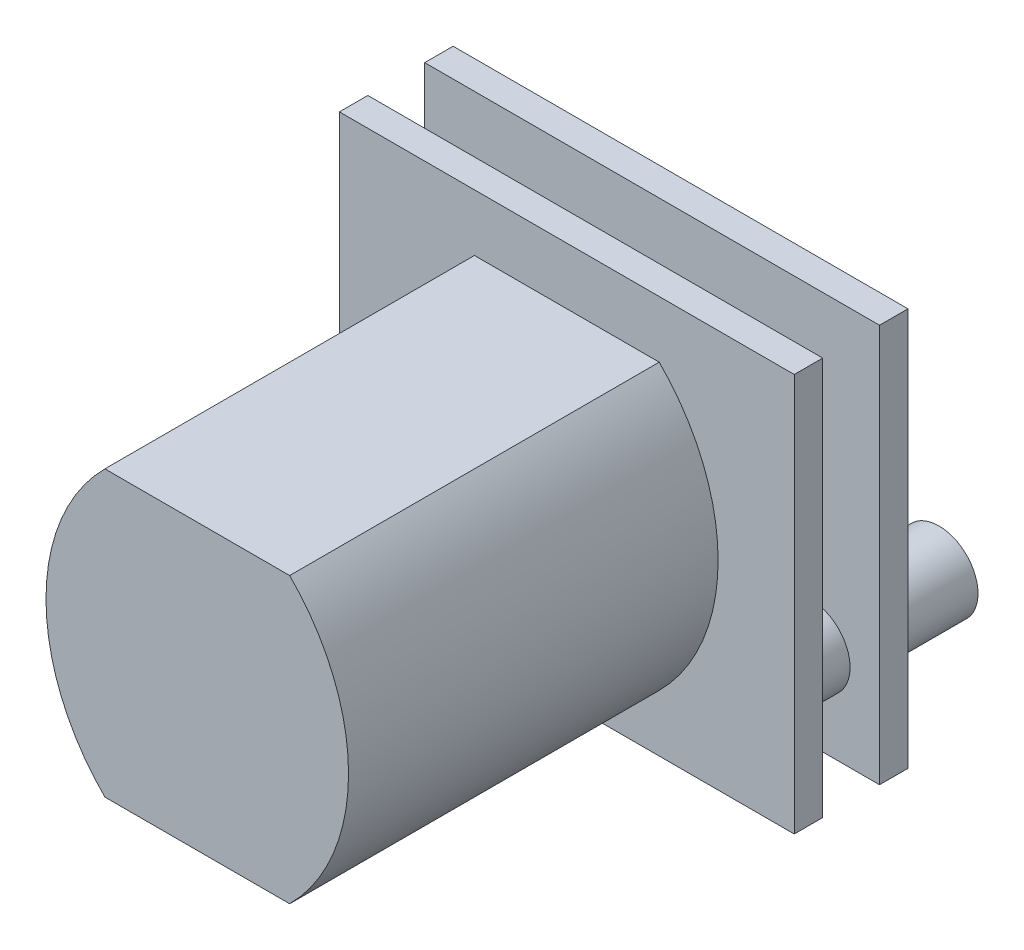
SolidWorks part; units mm, degrees
ref_plane "Front Plane" through (0, 0, 0) normal (0, 0, 1) x (1, 0, 0)
ref_plane "Top Plane" through (0, 0, 0) normal (0, 1, 0) x (1, 0, 0)
ref_plane "Right Plane" through (0, 0, 0) normal (1, 0, 0) x (0, 0, -1)
sketch "Sketch1" plane through (0, 0, 0) normal (0, 0, 1) x (1, 0, 0)
  line L0 (0, 0) -> (0, -50000) construction
  line L1 (-3.25, 5) -> (3.25, 5)
  line L3 (-3.25, -5) -> (3.25, -5)
  line L5 (-3.25, 5) -> (3.25, -5) construction
  line L6 (-3.25, -5) -> (3.25, 5) construction
  arc A0 (3.25, -5) -> (3.25, 5) centre (-1.75, 0) ccw
  arc A1 (-3.25, -5) -> (-3.25, 5) centre (1.75, 0) cw
  point P0 (0, 0)
  dimension "D1" = 6.5
  dimension "D2" = 10
extrude "Extrude1" add sketch "Sketch1" along normal blind 13
sketch "Sketch2" plane through (0, 0, 0) normal (0, 0, -1) x (-1, 0, 0)
  line L1 (8, -7) -> (-8, -7)
  line L2 (8, -7) -> (8, 7)
  line L3 (8, 7) -> (-8, 7)
  line L4 (-8, -7) -> (-8, 7)
  line L5 (8, -7) -> (-8, 7) construction
  line L6 (8, 7) -> (-8, -7) construction
  point P0 (0, 0)
  dimension "D1" = 8
  dimension "D2" = 7
extrude "Extrude2" add sketch "Sketch2" along normal blind 1
sketch "Sketch3" plane through (0, 0, -1) normal (0, 0, -1) x (-1, 0, 0)
  circle A0 centre (0, 0) radius 2.2487
extrude "Extrude3" add sketch "Sketch3" along normal blind 1.2
sketch "Sketch4" plane through (0, 0, -2.2) normal (0, 0, -1) x (-1, 0, 0)
  line L0 (-0.4598, -1.9553) -> (-0.6222, -2.4282)
  line L1 (0.2, -1.9987) -> (-0.2, -1.9987)
  line L2 (0.2, -1.9987) -> (0.2, -2.4987)
  line L3 (0.2, -2.4987) -> (-0.2, -2.4987)
  line L4 (-0.2, -1.9987) -> (-0.2, -2.4987)
  line L5 (0.2, -1.9987) -> (-0.2, -2.4987) construction
  line L6 (0.2, -2.4987) -> (-0.2, -1.9987) construction
  line L7 (-0.6222, -2.4282) -> (-1.0005, -2.2984)
  line L8 (-0.8381, -1.8254) -> (-1.0005, -2.2984)
  line L9 (-0.4598, -1.9553) -> (-0.8381, -1.8254)
  line L10 (-1.0698, -1.7001) -> (-1.3769, -2.0946)
  line L11 (-1.3769, -2.0946) -> (-1.6925, -1.849)
  line L12 (-1.3854, -1.4544) -> (-1.6925, -1.849)
  line L13 (-1.0698, -1.7001) -> (-1.3854, -1.4544)
  line L14 (-1.5638, -1.2606) -> (-1.9824, -1.5341)
  line L15 (-1.9824, -1.5341) -> (-2.2012, -1.1992)
  line L16 (-1.7826, -0.9257) -> (-2.2012, -1.1992)
  line L17 (-1.5638, -1.2606) -> (-1.7826, -0.9257)
  line L18 (-1.8884, -0.6845) -> (-2.3731, -0.8073)
  line L19 (-2.3731, -0.8073) -> (-2.4713, -0.4195)
  line L20 (-1.9866, -0.2968) -> (-2.4713, -0.4195)
  line L21 (-1.8884, -0.6845) -> (-1.9866, -0.2968)
  line L22 (-2.0084, -0.0343) -> (-2.5067, 0.007)
  line L23 (-2.5067, 0.007) -> (-2.4736, 0.4057)
  line L24 (-1.9753, 0.3644) -> (-2.4736, 0.4057)
  line L25 (-2.0084, -0.0343) -> (-1.9753, 0.3644)
  line L26 (-1.9107, 0.6197) -> (-2.3686, 0.8206)
  line L27 (-2.3686, 0.8206) -> (-2.2079, 1.1869)
  line L28 (-1.75, 0.986) -> (-2.2079, 1.1869)
  line L29 (-1.9107, 0.6197) -> (-1.75, 0.986)
  line L30 (-1.6059, 1.2065) -> (-1.9738, 1.5452)
  line L31 (-1.9738, 1.5452) -> (-1.7029, 1.8395)
  line L32 (-1.335, 1.5008) -> (-1.7029, 1.8395)
  line L33 (-1.6059, 1.2065) -> (-1.335, 1.5008)
  line L34 (-1.1272, 1.6626) -> (-1.3651, 2.1023)
  line L35 (-1.3651, 2.1023) -> (-1.0133, 2.2927)
  line L36 (-0.7754, 1.853) -> (-1.0133, 2.2927)
  line L37 (-1.1272, 1.6626) -> (-0.7754, 1.853)
  line L38 (-0.5262, 1.9385) -> (-0.6085, 2.4317)
  line L39 (-0.6085, 2.4317) -> (-0.214, 2.4975)
  line L40 (-0.1317, 2.0043) -> (-0.214, 2.4975)
  line L41 (-0.5262, 1.9385) -> (-0.1317, 2.0043)
  line L42 (0.1317, 2.0043) -> (0.214, 2.4975)
  line L43 (0.214, 2.4975) -> (0.6085, 2.4317)
  line L44 (0.5262, 1.9385) -> (0.6085, 2.4317)
  line L45 (0.1317, 2.0043) -> (0.5262, 1.9385)
  line L46 (0.7754, 1.853) -> (1.0133, 2.2927)
  line L47 (1.0133, 2.2927) -> (1.3651, 2.1023)
  line L48 (1.1272, 1.6626) -> (1.3651, 2.1023)
  line L49 (0.7754, 1.853) -> (1.1272, 1.6626)
  line L50 (1.335, 1.5008) -> (1.7029, 1.8395)
  line L51 (1.7029, 1.8395) -> (1.9738, 1.5452)
  line L52 (1.6059, 1.2065) -> (1.9738, 1.5452)
  line L53 (1.335, 1.5008) -> (1.6059, 1.2065)
  line L54 (1.75, 0.986) -> (2.2079, 1.1869)
  line L55 (2.2079, 1.1869) -> (2.3686, 0.8206)
  line L56 (1.9107, 0.6197) -> (2.3686, 0.8206)
  line L57 (1.75, 0.986) -> (1.9107, 0.6197)
  line L58 (1.9753, 0.3644) -> (2.4736, 0.4057)
  line L59 (2.4736, 0.4057) -> (2.5067, 0.007)
  line L60 (2.0084, -0.0343) -> (2.5067, 0.007)
  line L61 (1.9753, 0.3644) -> (2.0084, -0.0343)
  line L62 (1.9866, -0.2968) -> (2.4713, -0.4195)
  line L63 (2.4713, -0.4195) -> (2.3731, -0.8073)
  line L64 (1.8884, -0.6845) -> (2.3731, -0.8073)
  line L65 (1.9866, -0.2968) -> (1.8884, -0.6845)
  line L66 (1.7826, -0.9257) -> (2.2012, -1.1992)
  line L67 (2.2012, -1.1992) -> (1.9824, -1.5341)
  line L68 (1.5638, -1.2606) -> (1.9824, -1.5341)
  line L69 (1.7826, -0.9257) -> (1.5638, -1.2606)
  line L70 (1.3854, -1.4544) -> (1.6925, -1.849)
  line L71 (1.6925, -1.849) -> (1.3769, -2.0946)
  line L72 (1.0698, -1.7001) -> (1.3769, -2.0946)
  line L73 (1.3854, -1.4544) -> (1.0698, -1.7001)
  line L74 (0.8381, -1.8254) -> (1.0005, -2.2984)
  line L75 (1.0005, -2.2984) -> (0.6222, -2.4282)
  line L76 (0.4598, -1.9553) -> (0.6222, -2.4282)
  line L77 (0.8381, -1.8254) -> (0.4598, -1.9553)
  circle A0 centre (0, 0) radius 2.2487 construction
  point P0 (0, -2.2487)
  dimension "D1" = 0.5
  dimension "D2" = 0.4
extrude "Extrude4" cut sketch "Sketch4" against normal blind 1.2
sketch "Sketch5" plane through (0, 0, -1) normal (0, 0, -1) x (-1, 0, 0)
  circle A0 centre (-5.5906, -3.9415) radius 1.373
extrude "Extrude5" add sketch "Sketch5" along normal blind 2
sketch "Sketch6" plane through (0, 0, -3) normal (0, 0, -1) x (-1, 0, 0)
  line L1 (8, 7) -> (-8, 7)
  line L2 (8, 7) -> (8, -7)
  line L3 (8, -7) -> (-8, -7)
  line L4 (-8, 7) -> (-8, -7)
  line L5 (8, 7) -> (-8, -7) construction
  line L6 (8, -7) -> (-8, 7) construction
  point P0 (0, 0)
extrude "Extrude6" add sketch "Sketch6" along normal blind 1
sketch "Sketch7" plane through (0, 0, -4) normal (0, 0, -1) x (-1, 0, 0)
  circle A0 centre (-5.5906, -3.9415) radius 1.373
  circle A1 centre (-5.5906, -3.9415) radius 1.373 construction
extrude "Extrude7" add sketch "Sketch7" along normal blind 3.5
sketch "Sketch8" plane through (0, 0, -4) normal (0, 0, -1) x (-1, 0, 0)
  circle A0 centre (0, 0) radius 1.7339
extrude "Extrude8" add sketch "Sketch8" along normal blind 1.2
sketch "Sketch9" plane through (0, 0, -5.2) normal (0, 0, -1) x (-1, 0, 0)
  line L0 (1.84, -0.4231) -> (1.4874, -0.5539) construction
  line L1 (1.8847, 0.1125) -> (1.5832, 0.1125)
  line L2 (1.8847, 0.1125) -> (1.8847, -0.1125)
  line L3 (1.8847, -0.1125) -> (1.5832, -0.1125)
  line L4 (1.5832, 0.1125) -> (1.5832, -0.1125)
  line L5 (1.8847, 0.1125) -> (1.5832, -0.1125) construction
  line L6 (1.8847, -0.1125) -> (1.5832, 0.1125) construction
  line L7 (1.7767, -0.6389) -> (1.5507, -0.3381) construction
  line L8 (1.84, -0.4231) -> (1.7767, -0.6389)
  line L9 (1.84, -0.4231) -> (1.5507, -0.3381)
  line L10 (1.5507, -0.3381) -> (1.4874, -0.5539)
  line L11 (1.7767, -0.6389) -> (1.4874, -0.5539)
  line L12 (1.6463, -0.9243) -> (1.2711, -0.9505) construction
  line L13 (1.5247, -1.1135) -> (1.3926, -0.7613) construction
  line L14 (1.6463, -0.9243) -> (1.5247, -1.1135)
  line L15 (1.6463, -0.9243) -> (1.3926, -0.7613)
  line L16 (1.3926, -0.7613) -> (1.2711, -0.9505)
  line L17 (1.5247, -1.1135) -> (1.2711, -0.9505)
  line L18 (1.3192, -1.3507) -> (0.9518, -1.2701) construction
  line L19 (1.1492, -1.498) -> (1.1217, -1.1228) construction
  line L20 (1.3192, -1.3507) -> (1.1492, -1.498)
  line L21 (1.3192, -1.3507) -> (1.1217, -1.1228)
  line L22 (1.1217, -1.1228) -> (0.9518, -1.2701)
  line L23 (1.1492, -1.498) -> (0.9518, -1.2701)
  line L24 (0.8852, -1.6677) -> (0.5554, -1.4868) construction
  line L25 (0.6806, -1.7611) -> (0.76, -1.3934) construction
  line L26 (0.8852, -1.6677) -> (0.6806, -1.7611)
  line L27 (0.8852, -1.6677) -> (0.76, -1.3934)
  line L28 (0.76, -1.3934) -> (0.5554, -1.4868)
  line L29 (0.6806, -1.7611) -> (0.5554, -1.4868)
  line L30 (0.3795, -1.8495) -> (0.114, -1.5831) construction
  line L31 (0.1569, -1.8815) -> (0.3366, -1.5511) construction
  line L32 (0.3795, -1.8495) -> (0.1569, -1.8815)
  line L33 (0.3795, -1.8495) -> (0.3366, -1.5511)
  line L34 (0.3366, -1.5511) -> (0.114, -1.5831)
  line L35 (0.1569, -1.8815) -> (0.114, -1.5831)
  line L36 (-0.1569, -1.8815) -> (-0.3366, -1.5511) construction
  line L37 (-0.3795, -1.8495) -> (-0.114, -1.5831) construction
  line L38 (-0.1569, -1.8815) -> (-0.3795, -1.8495)
  line L39 (-0.1569, -1.8815) -> (-0.114, -1.5831)
  line L40 (-0.114, -1.5831) -> (-0.3366, -1.5511)
  line L41 (-0.3795, -1.8495) -> (-0.3366, -1.5511)
  line L42 (-0.6806, -1.7611) -> (-0.76, -1.3934) construction
  line L43 (-0.8852, -1.6677) -> (-0.5554, -1.4868) construction
  line L44 (-0.6806, -1.7611) -> (-0.8852, -1.6677)
  line L45 (-0.6806, -1.7611) -> (-0.5554, -1.4868)
  line L46 (-0.5554, -1.4868) -> (-0.76, -1.3934)
  line L47 (-0.8852, -1.6677) -> (-0.76, -1.3934)
  line L48 (-1.1492, -1.498) -> (-1.1217, -1.1228) construction
  line L49 (-1.3192, -1.3507) -> (-0.9518, -1.2701) construction
  line L50 (-1.1492, -1.498) -> (-1.3192, -1.3507)
  line L51 (-1.1492, -1.498) -> (-0.9518, -1.2701)
  line L52 (-0.9518, -1.2701) -> (-1.1217, -1.1228)
  line L53 (-1.3192, -1.3507) -> (-1.1217, -1.1228)
  line L54 (-1.5247, -1.1135) -> (-1.3926, -0.7613) construction
  line L55 (-1.6463, -0.9243) -> (-1.2711, -0.9505) construction
  line L56 (-1.5247, -1.1135) -> (-1.6463, -0.9243)
  line L57 (-1.5247, -1.1135) -> (-1.2711, -0.9505)
  line L58 (-1.2711, -0.9505) -> (-1.3926, -0.7613)
  line L59 (-1.6463, -0.9243) -> (-1.3926, -0.7613)
  line L60 (-1.7767, -0.6389) -> (-1.5507, -0.3381) construction
  line L61 (-1.84, -0.4231) -> (-1.4874, -0.5539) construction
  line L62 (-1.7767, -0.6389) -> (-1.84, -0.4231)
  line L63 (-1.7767, -0.6389) -> (-1.4874, -0.5539)
  line L64 (-1.4874, -0.5539) -> (-1.5507, -0.3381)
  line L65 (-1.84, -0.4231) -> (-1.5507, -0.3381)
  line L66 (-1.8847, -0.1125) -> (-1.5832, 0.1125) construction
  line L67 (-1.8847, 0.1125) -> (-1.5832, -0.1125) construction
  line L68 (-1.8847, -0.1125) -> (-1.8847, 0.1125)
  line L69 (-1.8847, -0.1125) -> (-1.5832, -0.1125)
  line L70 (-1.5832, -0.1125) -> (-1.5832, 0.1125)
  line L71 (-1.8847, 0.1125) -> (-1.5832, 0.1125)
  line L72 (-1.84, 0.4231) -> (-1.4874, 0.5539) construction
  line L73 (-1.7767, 0.6389) -> (-1.5507, 0.3381) construction
  line L74 (-1.84, 0.4231) -> (-1.7767, 0.6389)
  line L75 (-1.84, 0.4231) -> (-1.5507, 0.3381)
  line L76 (-1.5507, 0.3381) -> (-1.4874, 0.5539)
  line L77 (-1.7767, 0.6389) -> (-1.4874, 0.5539)
  line L78 (-1.6463, 0.9243) -> (-1.2711, 0.9505) construction
  line L79 (-1.5247, 1.1135) -> (-1.3926, 0.7613) construction
  line L80 (-1.6463, 0.9243) -> (-1.5247, 1.1135)
  line L81 (-1.6463, 0.9243) -> (-1.3926, 0.7613)
  line L82 (-1.3926, 0.7613) -> (-1.2711, 0.9505)
  line L83 (-1.5247, 1.1135) -> (-1.2711, 0.9505)
  line L84 (-1.3192, 1.3507) -> (-0.9518, 1.2701) construction
  line L85 (-1.1492, 1.498) -> (-1.1217, 1.1228) construction
  line L86 (-1.3192, 1.3507) -> (-1.1492, 1.498)
  line L87 (-1.3192, 1.3507) -> (-1.1217, 1.1228)
  line L88 (-1.1217, 1.1228) -> (-0.9518, 1.2701)
  line L89 (-1.1492, 1.498) -> (-0.9518, 1.2701)
  line L90 (-0.8852, 1.6677) -> (-0.5554, 1.4868) construction
  line L91 (-0.6806, 1.7611) -> (-0.76, 1.3934) construction
  line L92 (-0.8852, 1.6677) -> (-0.6806, 1.7611)
  line L93 (-0.8852, 1.6677) -> (-0.76, 1.3934)
  line L94 (-0.76, 1.3934) -> (-0.5554, 1.4868)
  line L95 (-0.6806, 1.7611) -> (-0.5554, 1.4868)
  line L96 (-0.3795, 1.8495) -> (-0.114, 1.5831) construction
  line L97 (-0.1569, 1.8815) -> (-0.3366, 1.5511) construction
  line L98 (-0.3795, 1.8495) -> (-0.1569, 1.8815)
  line L99 (-0.3795, 1.8495) -> (-0.3366, 1.5511)
  line L100 (-0.3366, 1.5511) -> (-0.114, 1.5831)
  line L101 (-0.1569, 1.8815) -> (-0.114, 1.5831)
  line L102 (0.1569, 1.8815) -> (0.3366, 1.5511) construction
  line L103 (0.3795, 1.8495) -> (0.114, 1.5831) construction
  line L104 (0.1569, 1.8815) -> (0.3795, 1.8495)
  line L105 (0.1569, 1.8815) -> (0.114, 1.5831)
  line L106 (0.114, 1.5831) -> (0.3366, 1.5511)
  line L107 (0.3795, 1.8495) -> (0.3366, 1.5511)
  line L108 (0.6806, 1.7611) -> (0.76, 1.3934) construction
  line L109 (0.8852, 1.6677) -> (0.5554, 1.4868) construction
  line L110 (0.6806, 1.7611) -> (0.8852, 1.6677)
  line L111 (0.6806, 1.7611) -> (0.5554, 1.4868)
  line L112 (0.5554, 1.4868) -> (0.76, 1.3934)
  line L113 (0.8852, 1.6677) -> (0.76, 1.3934)
  line L114 (1.1492, 1.498) -> (1.1217, 1.1228) construction
  line L115 (1.3192, 1.3507) -> (0.9518, 1.2701) construction
  line L116 (1.1492, 1.498) -> (1.3192, 1.3507)
  line L117 (1.1492, 1.498) -> (0.9518, 1.2701)
  line L118 (0.9518, 1.2701) -> (1.1217, 1.1228)
  line L119 (1.3192, 1.3507) -> (1.1217, 1.1228)
  line L120 (1.5247, 1.1135) -> (1.3926, 0.7613) construction
  line L121 (1.6463, 0.9243) -> (1.2711, 0.9505) construction
  line L122 (1.5247, 1.1135) -> (1.6463, 0.9243)
  line L123 (1.5247, 1.1135) -> (1.2711, 0.9505)
  line L124 (1.2711, 0.9505) -> (1.3926, 0.7613)
  line L125 (1.6463, 0.9243) -> (1.3926, 0.7613)
  line L126 (1.7767, 0.6389) -> (1.5507, 0.3381) construction
  line L127 (1.84, 0.4231) -> (1.4874, 0.5539) construction
  line L128 (1.7767, 0.6389) -> (1.84, 0.4231)
  line L129 (1.7767, 0.6389) -> (1.4874, 0.5539)
  line L130 (1.4874, 0.5539) -> (1.5507, 0.3381)
  line L131 (1.84, 0.4231) -> (1.5507, 0.3381)
  circle A0 centre (0, 0) radius 1.7339 construction
  point P0 (1.7339, 0)
  point P10 (1.6637, -0.4885)
  point P15 (1.4587, -0.9374)
  point P20 (1.1355, -1.3104)
  point P25 (0.7203, -1.5772)
  point P30 (0.2468, -1.7163)
  point P35 (-0.2468, -1.7163)
  point P40 (-0.7203, -1.5772)
  point P45 (-1.1355, -1.3104)
  point P50 (-1.4587, -0.9374)
  point P55 (-1.6637, -0.4885)
  point P60 (-1.7339, 0)
  point P65 (-1.6637, 0.4885)
  point P70 (-1.4587, 0.9374)
  point P75 (-1.1355, 1.3104)
  point P80 (-0.7203, 1.5772)
  point P85 (-0.2468, 1.7163)
  point P90 (0.2468, 1.7163)
  point P95 (0.7203, 1.5772)
  point P100 (1.1355, 1.3104)
  point P105 (1.4587, 0.9374)
  point P110 (1.6637, 0.4885)
extrude "Extrude9" cut sketch "Sketch9" against normal blind 1.2
sketch "Sketch10" plane through (0, -5, 0) normal (0, -1, 0) x (1, 0, 0)
  line L0 (-1.1258, 2.827) -> (-1.9264, 8.9482) construction
  line L1 (1.8742, 2.827) -> (1.0736, 2.827)
  line L2 (1.8742, 2.827) -> (1.8742, 8.9482)
  line L3 (1.8742, 8.9482) -> (1.0736, 8.9482)
  line L4 (1.0736, 2.827) -> (1.0736, 8.9482)
  line L5 (1.8742, 2.827) -> (1.0736, 8.9482) construction
  line L6 (1.8742, 8.9482) -> (1.0736, 2.827) construction
  line L7 (-1.1258, 8.9482) -> (-1.9264, 2.827) construction
  line L8 (-1.1258, 2.827) -> (-1.1258, 8.9482)
  line L9 (-1.1258, 2.827) -> (-1.9264, 2.827)
  line L10 (-1.9264, 2.827) -> (-1.9264, 8.9482)
  line L11 (-1.1258, 8.9482) -> (-1.9264, 8.9482)
  point P0 (1.4739, 5.8876)
  point P7 (-1.5261, 5.8876)
extrude "Extrude10" cut sketch "Sketch10" against normal blind 1.2
sketch "Sketch11" plane through (0, 0, -5.2) normal (0, 0, -1) x (-1, 0, 0)
  circle A0 centre (0, 0) radius 0.6011
extrude "Extrude11" add sketch "Sketch11" along normal blind 1.2
sketch "Sketch12" plane through (0, 0, -6.4) normal (0, 0, -1) x (-1, 0, 0)
  line L0 (-0.4987, 0.1186) -> (-0.631, 0.2926) construction
  line L1 (-0.5092, -0.0591) -> (-0.693, -0.0591)
  line L2 (-0.5092, -0.0591) -> (-0.5092, 0.0591)
  line L3 (-0.5092, 0.0591) -> (-0.693, 0.0591)
  line L4 (-0.693, -0.0591) -> (-0.693, 0.0591)
  line L5 (-0.5092, -0.0591) -> (-0.693, 0.0591) construction
  line L6 (-0.5092, 0.0591) -> (-0.693, -0.0591) construction
  line L7 (-0.4583, 0.2297) -> (-0.6714, 0.1815) construction
  line L8 (-0.4987, 0.1186) -> (-0.4583, 0.2297)
  line L9 (-0.4987, 0.1186) -> (-0.6714, 0.1815)
  line L10 (-0.6714, 0.1815) -> (-0.631, 0.2926)
  line L11 (-0.4583, 0.2297) -> (-0.631, 0.2926)
  line L12 (-0.4281, 0.282) -> (-0.4929, 0.4907) construction
  line L13 (-0.3521, 0.3726) -> (-0.5688, 0.4002) construction
  line L14 (-0.4281, 0.282) -> (-0.3521, 0.3726)
  line L15 (-0.4281, 0.282) -> (-0.5688, 0.4002)
  line L16 (-0.5688, 0.4002) -> (-0.4929, 0.4907)
  line L17 (-0.3521, 0.3726) -> (-0.4929, 0.4907)
  line L18 (-0.3058, 0.4114) -> (-0.2953, 0.6297) construction
  line L19 (-0.2034, 0.4705) -> (-0.3977, 0.5706) construction
  line L20 (-0.3058, 0.4114) -> (-0.2034, 0.4705)
  line L21 (-0.3058, 0.4114) -> (-0.3977, 0.5706)
  line L22 (-0.3977, 0.5706) -> (-0.2953, 0.6297)
  line L23 (-0.2034, 0.4705) -> (-0.2953, 0.6297)
  line L24 (-0.1466, 0.4912) -> (-0.0621, 0.6927) construction
  line L25 (-0.0302, 0.5117) -> (-0.1785, 0.6722) construction
  line L26 (-0.1466, 0.4912) -> (-0.0302, 0.5117)
  line L27 (-0.1466, 0.4912) -> (-0.1785, 0.6722)
  line L28 (-0.1785, 0.6722) -> (-0.0621, 0.6927)
  line L29 (-0.0302, 0.5117) -> (-0.0621, 0.6927)
  line L30 (0.0302, 0.5117) -> (0.1785, 0.6722) construction
  line L31 (0.1466, 0.4912) -> (0.0621, 0.6927) construction
  line L32 (0.0302, 0.5117) -> (0.1466, 0.4912)
  line L33 (0.0302, 0.5117) -> (0.0621, 0.6927)
  line L34 (0.0621, 0.6927) -> (0.1785, 0.6722)
  line L35 (0.1466, 0.4912) -> (0.1785, 0.6722)
  line L36 (0.2034, 0.4705) -> (0.3977, 0.5706) construction
  line L37 (0.3058, 0.4114) -> (0.2953, 0.6297) construction
  line L38 (0.2034, 0.4705) -> (0.3058, 0.4114)
  line L39 (0.2034, 0.4705) -> (0.2953, 0.6297)
  line L40 (0.2953, 0.6297) -> (0.3977, 0.5706)
  line L41 (0.3058, 0.4114) -> (0.3977, 0.5706)
  line L42 (0.3521, 0.3726) -> (0.5688, 0.4002) construction
  line L43 (0.4281, 0.282) -> (0.4929, 0.4907) construction
  line L44 (0.3521, 0.3726) -> (0.4281, 0.282)
  line L45 (0.3521, 0.3726) -> (0.4929, 0.4907)
  line L46 (0.4929, 0.4907) -> (0.5688, 0.4002)
  line L47 (0.4281, 0.282) -> (0.5688, 0.4002)
  line L48 (0.4583, 0.2297) -> (0.6714, 0.1815) construction
  line L49 (0.4987, 0.1186) -> (0.631, 0.2926) construction
  line L50 (0.4583, 0.2297) -> (0.4987, 0.1186)
  line L51 (0.4583, 0.2297) -> (0.631, 0.2926)
  line L52 (0.631, 0.2926) -> (0.6714, 0.1815)
  line L53 (0.4987, 0.1186) -> (0.6714, 0.1815)
  line L54 (0.5092, 0.0591) -> (0.693, -0.0591) construction
  line L55 (0.5092, -0.0591) -> (0.693, 0.0591) construction
  line L56 (0.5092, 0.0591) -> (0.5092, -0.0591)
  line L57 (0.5092, 0.0591) -> (0.693, 0.0591)
  line L58 (0.693, 0.0591) -> (0.693, -0.0591)
  line L59 (0.5092, -0.0591) -> (0.693, -0.0591)
  line L60 (0.4987, -0.1186) -> (0.631, -0.2926) construction
  line L61 (0.4583, -0.2297) -> (0.6714, -0.1815) construction
  line L62 (0.4987, -0.1186) -> (0.4583, -0.2297)
  line L63 (0.4987, -0.1186) -> (0.6714, -0.1815)
  line L64 (0.6714, -0.1815) -> (0.631, -0.2926)
  line L65 (0.4583, -0.2297) -> (0.631, -0.2926)
  line L66 (0.4281, -0.282) -> (0.4929, -0.4907) construction
  line L67 (0.3521, -0.3726) -> (0.5688, -0.4002) construction
  line L68 (0.4281, -0.282) -> (0.3521, -0.3726)
  line L69 (0.4281, -0.282) -> (0.5688, -0.4002)
  line L70 (0.5688, -0.4002) -> (0.4929, -0.4907)
  line L71 (0.3521, -0.3726) -> (0.4929, -0.4907)
  line L72 (0.3058, -0.4114) -> (0.2953, -0.6297) construction
  line L73 (0.2034, -0.4705) -> (0.3977, -0.5706) construction
  line L74 (0.3058, -0.4114) -> (0.2034, -0.4705)
  line L75 (0.3058, -0.4114) -> (0.3977, -0.5706)
  line L76 (0.3977, -0.5706) -> (0.2953, -0.6297)
  line L77 (0.2034, -0.4705) -> (0.2953, -0.6297)
  line L78 (0.1466, -0.4912) -> (0.0621, -0.6927) construction
  line L79 (0.0302, -0.5117) -> (0.1785, -0.6722) construction
  line L80 (0.1466, -0.4912) -> (0.0302, -0.5117)
  line L81 (0.1466, -0.4912) -> (0.1785, -0.6722)
  line L82 (0.1785, -0.6722) -> (0.0621, -0.6927)
  line L83 (0.0302, -0.5117) -> (0.0621, -0.6927)
  line L84 (-0.0302, -0.5117) -> (-0.1785, -0.6722) construction
  line L85 (-0.1466, -0.4912) -> (-0.0621, -0.6927) construction
  line L86 (-0.0302, -0.5117) -> (-0.1466, -0.4912)
  line L87 (-0.0302, -0.5117) -> (-0.0621, -0.6927)
  line L88 (-0.0621, -0.6927) -> (-0.1785, -0.6722)
  line L89 (-0.1466, -0.4912) -> (-0.1785, -0.6722)
  line L90 (-0.2034, -0.4705) -> (-0.3977, -0.5706) construction
  line L91 (-0.3058, -0.4114) -> (-0.2953, -0.6297) construction
  line L92 (-0.2034, -0.4705) -> (-0.3058, -0.4114)
  line L93 (-0.2034, -0.4705) -> (-0.2953, -0.6297)
  line L94 (-0.2953, -0.6297) -> (-0.3977, -0.5706)
  line L95 (-0.3058, -0.4114) -> (-0.3977, -0.5706)
  line L96 (-0.3521, -0.3726) -> (-0.5688, -0.4002) construction
  line L97 (-0.4281, -0.282) -> (-0.4929, -0.4907) construction
  line L98 (-0.3521, -0.3726) -> (-0.4281, -0.282)
  line L99 (-0.3521, -0.3726) -> (-0.4929, -0.4907)
  line L100 (-0.4929, -0.4907) -> (-0.5688, -0.4002)
  line L101 (-0.4281, -0.282) -> (-0.5688, -0.4002)
  line L102 (-0.4583, -0.2297) -> (-0.6714, -0.1815) construction
  line L103 (-0.4987, -0.1186) -> (-0.631, -0.2926) construction
  line L104 (-0.4583, -0.2297) -> (-0.4987, -0.1186)
  line L105 (-0.4583, -0.2297) -> (-0.631, -0.2926)
  line L106 (-0.631, -0.2926) -> (-0.6714, -0.1815)
  line L107 (-0.4987, -0.1186) -> (-0.6714, -0.1815)
  circle A0 centre (0, 0) radius 0.6011 construction
  point P0 (-0.6011, 0)
  point P9 (-0.5648, 0.2056)
  point P14 (-0.4605, 0.3864)
  point P19 (-0.3005, 0.5206)
  point P24 (-0.1044, 0.592)
  point P29 (0.1044, 0.592)
  point P34 (0.3005, 0.5206)
  point P39 (0.4605, 0.3864)
  point P44 (0.5648, 0.2056)
  point P49 (0.6011, 0)
  point P54 (0.5648, -0.2056)
  point P59 (0.4605, -0.3864)
  point P64 (0.3005, -0.5206)
  point P69 (0.1044, -0.592)
  point P74 (-0.1044, -0.592)
  point P79 (-0.3005, -0.5206)
  point P84 (-0.4605, -0.3864)
  point P89 (-0.5648, -0.2056)
extrude "Extrude12" cut sketch "Sketch12" against normal blind 1.2
sketch "Sketch13" plane through (0, 0, -6.4) normal (0, 0, -1) x (-1, 0, 0)
  circle A0 centre (0, 0) radius 2.1614
extrude "Extrude13" add sketch "Sketch13" along normal blind 1.2
sketch "Sketch14" plane through (0, 0, -7.6) normal (0, 0, -1) x (-1, 0, 0)
  line L0 (-2.3499, 0.4749) -> (-1.8473, 0.5596) construction
  line L1 (-2.3953, -0.1013) -> (-1.9276, -0.1013)
  line L2 (-2.3953, -0.1013) -> (-2.3953, 0.1013)
  line L3 (-2.3953, 0.1013) -> (-1.9276, 0.1013)
  line L4 (-1.9276, -0.1013) -> (-1.9276, 0.1013)
  line L5 (-2.3953, -0.1013) -> (-1.9276, 0.1013) construction
  line L6 (-2.3953, 0.1013) -> (-1.9276, -0.1013) construction
  line L7 (-2.3014, 0.6716) -> (-1.8958, 0.363) construction
  line L8 (-2.3499, 0.4749) -> (-2.3014, 0.6716)
  line L9 (-2.3499, 0.4749) -> (-1.8958, 0.363)
  line L10 (-1.8958, 0.363) -> (-1.8473, 0.5596)
  line L11 (-2.3014, 0.6716) -> (-1.8473, 0.5596)
  line L12 (-2.168, 1.0235) -> (-1.6597, 0.9855) construction
  line L13 (-2.0738, 1.2028) -> (-1.7538, 0.8061) construction
  line L14 (-2.168, 1.0235) -> (-2.0738, 1.2028)
  line L15 (-2.168, 1.0235) -> (-1.7538, 0.8061)
  line L16 (-1.7538, 0.8061) -> (-1.6597, 0.9855)
  line L17 (-2.0738, 1.2028) -> (-1.6597, 0.9855)
  line L18 (-1.8601, 1.5125) -> (-1.3756, 1.354) construction
  line L19 (-1.7257, 1.6642) -> (-1.51, 1.2024) construction
  line L20 (-1.8601, 1.5125) -> (-1.7257, 1.6642)
  line L21 (-1.8601, 1.5125) -> (-1.51, 1.2024)
  line L22 (-1.51, 1.2024) -> (-1.3756, 1.354)
  line L23 (-1.7257, 1.6642) -> (-1.3756, 1.354)
  line L24 (-1.444, 1.9137) -> (-1.0116, 1.6439) construction
  line L25 (-1.2773, 2.0288) -> (-1.1783, 1.5288) construction
  line L26 (-1.444, 1.9137) -> (-1.2773, 2.0288)
  line L27 (-1.444, 1.9137) -> (-1.1783, 1.5288)
  line L28 (-1.1783, 1.5288) -> (-1.0116, 1.6439)
  line L29 (-1.2773, 2.0288) -> (-1.0116, 1.6439)
  line L30 (-0.9441, 2.2037) -> (-0.5888, 1.8382) construction
  line L31 (-0.7547, 2.2755) -> (-0.7782, 1.7664) construction
  line L32 (-0.9441, 2.2037) -> (-0.7547, 2.2755)
  line L33 (-0.9441, 2.2037) -> (-0.7782, 1.7664)
  line L34 (-0.7782, 1.7664) -> (-0.5888, 1.8382)
  line L35 (-0.7547, 2.2755) -> (-0.5888, 1.8382)
  line L36 (-0.3893, 2.3656) -> (-0.1318, 1.9257) construction
  line L37 (-0.1882, 2.39) -> (-0.3329, 1.9013) construction
  line L38 (-0.3893, 2.3656) -> (-0.1882, 2.39)
  line L39 (-0.3893, 2.3656) -> (-0.3329, 1.9013)
  line L40 (-0.3329, 1.9013) -> (-0.1318, 1.9257)
  line L41 (-0.1882, 2.39) -> (-0.1318, 1.9257)
  line L42 (0.1882, 2.39) -> (0.3329, 1.9013) construction
  line L43 (0.3893, 2.3656) -> (0.1318, 1.9257) construction
  line L44 (0.1882, 2.39) -> (0.3893, 2.3656)
  line L45 (0.1882, 2.39) -> (0.1318, 1.9257)
  line L46 (0.1318, 1.9257) -> (0.3329, 1.9013)
  line L47 (0.3893, 2.3656) -> (0.3329, 1.9013)
  line L48 (0.7547, 2.2755) -> (0.7782, 1.7664) construction
  line L49 (0.9441, 2.2037) -> (0.5888, 1.8382) construction
  line L50 (0.7547, 2.2755) -> (0.9441, 2.2037)
  line L51 (0.7547, 2.2755) -> (0.5888, 1.8382)
  line L52 (0.5888, 1.8382) -> (0.7782, 1.7664)
  line L53 (0.9441, 2.2037) -> (0.7782, 1.7664)
  line L54 (1.2773, 2.0288) -> (1.1783, 1.5288) construction
  line L55 (1.444, 1.9137) -> (1.0116, 1.6439) construction
  line L56 (1.2773, 2.0288) -> (1.444, 1.9137)
  line L57 (1.2773, 2.0288) -> (1.0116, 1.6439)
  line L58 (1.0116, 1.6439) -> (1.1783, 1.5288)
  line L59 (1.444, 1.9137) -> (1.1783, 1.5288)
  line L60 (1.7257, 1.6642) -> (1.51, 1.2024) construction
  line L61 (1.8601, 1.5125) -> (1.3756, 1.354) construction
  line L62 (1.7257, 1.6642) -> (1.8601, 1.5125)
  line L63 (1.7257, 1.6642) -> (1.3756, 1.354)
  line L64 (1.3756, 1.354) -> (1.51, 1.2024)
  line L65 (1.8601, 1.5125) -> (1.51, 1.2024)
  line L66 (2.0738, 1.2028) -> (1.7538, 0.8061) construction
  line L67 (2.168, 1.0235) -> (1.6597, 0.9855) construction
  line L68 (2.0738, 1.2028) -> (2.168, 1.0235)
  line L69 (2.0738, 1.2028) -> (1.6597, 0.9855)
  line L70 (1.6597, 0.9855) -> (1.7538, 0.8061)
  line L71 (2.168, 1.0235) -> (1.7538, 0.8061)
  line L72 (2.3014, 0.6716) -> (1.8958, 0.363) construction
  line L73 (2.3499, 0.4749) -> (1.8473, 0.5596) construction
  line L74 (2.3014, 0.6716) -> (2.3499, 0.4749)
  line L75 (2.3014, 0.6716) -> (1.8473, 0.5596)
  line L76 (1.8473, 0.5596) -> (1.8958, 0.363)
  line L77 (2.3499, 0.4749) -> (1.8958, 0.363)
  line L78 (2.3953, 0.1013) -> (1.9276, -0.1013) construction
  line L79 (2.3953, -0.1013) -> (1.9276, 0.1013) construction
  line L80 (2.3953, 0.1013) -> (2.3953, -0.1013)
  line L81 (2.3953, 0.1013) -> (1.9276, 0.1013)
  line L82 (1.9276, 0.1013) -> (1.9276, -0.1013)
  line L83 (2.3953, -0.1013) -> (1.9276, -0.1013)
  line L84 (2.3499, -0.4749) -> (1.8473, -0.5596) construction
  line L85 (2.3014, -0.6716) -> (1.8958, -0.363) construction
  line L86 (2.3499, -0.4749) -> (2.3014, -0.6716)
  line L87 (2.3499, -0.4749) -> (1.8958, -0.363)
  line L88 (1.8958, -0.363) -> (1.8473, -0.5596)
  line L89 (2.3014, -0.6716) -> (1.8473, -0.5596)
  line L90 (2.168, -1.0235) -> (1.6597, -0.9855) construction
  line L91 (2.0738, -1.2028) -> (1.7538, -0.8061) construction
  line L92 (2.168, -1.0235) -> (2.0738, -1.2028)
  line L93 (2.168, -1.0235) -> (1.7538, -0.8061)
  line L94 (1.7538, -0.8061) -> (1.6597, -0.9855)
  line L95 (2.0738, -1.2028) -> (1.6597, -0.9855)
  line L96 (1.8601, -1.5125) -> (1.3756, -1.354) construction
  line L97 (1.7257, -1.6642) -> (1.51, -1.2024) construction
  line L98 (1.8601, -1.5125) -> (1.7257, -1.6642)
  line L99 (1.8601, -1.5125) -> (1.51, -1.2024)
  line L100 (1.51, -1.2024) -> (1.3756, -1.354)
  line L101 (1.7257, -1.6642) -> (1.3756, -1.354)
  line L102 (1.444, -1.9137) -> (1.0116, -1.6439) construction
  line L103 (1.2773, -2.0288) -> (1.1783, -1.5288) construction
  line L104 (1.444, -1.9137) -> (1.2773, -2.0288)
  line L105 (1.444, -1.9137) -> (1.1783, -1.5288)
  line L106 (1.1783, -1.5288) -> (1.0116, -1.6439)
  line L107 (1.2773, -2.0288) -> (1.0116, -1.6439)
  line L108 (0.9441, -2.2037) -> (0.5888, -1.8382) construction
  line L109 (0.7547, -2.2755) -> (0.7782, -1.7664) construction
  line L110 (0.9441, -2.2037) -> (0.7547, -2.2755)
  line L111 (0.9441, -2.2037) -> (0.7782, -1.7664)
  line L112 (0.7782, -1.7664) -> (0.5888, -1.8382)
  line L113 (0.7547, -2.2755) -> (0.5888, -1.8382)
  line L114 (0.3893, -2.3656) -> (0.1318, -1.9257) construction
  line L115 (0.1882, -2.39) -> (0.3329, -1.9013) construction
  line L116 (0.3893, -2.3656) -> (0.1882, -2.39)
  line L117 (0.3893, -2.3656) -> (0.3329, -1.9013)
  line L118 (0.3329, -1.9013) -> (0.1318, -1.9257)
  line L119 (0.1882, -2.39) -> (0.1318, -1.9257)
  line L120 (-0.1882, -2.39) -> (-0.3329, -1.9013) construction
  line L121 (-0.3893, -2.3656) -> (-0.1318, -1.9257) construction
  line L122 (-0.1882, -2.39) -> (-0.3893, -2.3656)
  line L123 (-0.1882, -2.39) -> (-0.1318, -1.9257)
  line L124 (-0.1318, -1.9257) -> (-0.3329, -1.9013)
  line L125 (-0.3893, -2.3656) -> (-0.3329, -1.9013)
  line L126 (-0.7547, -2.2755) -> (-0.7782, -1.7664) construction
  line L127 (-0.9441, -2.2037) -> (-0.5888, -1.8382) construction
  line L128 (-0.7547, -2.2755) -> (-0.9441, -2.2037)
  line L129 (-0.7547, -2.2755) -> (-0.5888, -1.8382)
  line L130 (-0.5888, -1.8382) -> (-0.7782, -1.7664)
  line L131 (-0.9441, -2.2037) -> (-0.7782, -1.7664)
  line L132 (-1.2773, -2.0288) -> (-1.1783, -1.5288) construction
  line L133 (-1.444, -1.9137) -> (-1.0116, -1.6439) construction
  line L134 (-1.2773, -2.0288) -> (-1.444, -1.9137)
  line L135 (-1.2773, -2.0288) -> (-1.0116, -1.6439)
  line L136 (-1.0116, -1.6439) -> (-1.1783, -1.5288)
  line L137 (-1.444, -1.9137) -> (-1.1783, -1.5288)
  line L138 (-1.7257, -1.6642) -> (-1.51, -1.2024) construction
  line L139 (-1.8601, -1.5125) -> (-1.3756, -1.354) construction
  line L140 (-1.7257, -1.6642) -> (-1.8601, -1.5125)
  line L141 (-1.7257, -1.6642) -> (-1.3756, -1.354)
  line L142 (-1.3756, -1.354) -> (-1.51, -1.2024)
  line L143 (-1.8601, -1.5125) -> (-1.51, -1.2024)
  line L144 (-2.0738, -1.2028) -> (-1.7538, -0.8061) construction
  line L145 (-2.168, -1.0235) -> (-1.6597, -0.9855) construction
  line L146 (-2.0738, -1.2028) -> (-2.168, -1.0235)
  line L147 (-2.0738, -1.2028) -> (-1.6597, -0.9855)
  line L148 (-1.6597, -0.9855) -> (-1.7538, -0.8061)
  line L149 (-2.168, -1.0235) -> (-1.7538, -0.8061)
  line L150 (-2.3014, -0.6716) -> (-1.8958, -0.363) construction
  line L151 (-2.3499, -0.4749) -> (-1.8473, -0.5596) construction
  line L152 (-2.3014, -0.6716) -> (-2.3499, -0.4749)
  line L153 (-2.3014, -0.6716) -> (-1.8473, -0.5596)
  line L154 (-1.8473, -0.5596) -> (-1.8958, -0.363)
  line L155 (-2.3499, -0.4749) -> (-1.8958, -0.363)
  circle A0 centre (0, 0) radius 2.1614 construction
  point P0 (-2.1614, 0)
  point P9 (-2.0986, 0.5173)
  point P14 (-1.9138, 1.0045)
  point P19 (-1.6178, 1.4333)
  point P24 (-1.2278, 1.7788)
  point P29 (-0.7665, 2.021)
  point P34 (-0.2605, 2.1457)
  point P39 (0.2605, 2.1457)
  point P44 (0.7665, 2.021)
  point P49 (1.2278, 1.7788)
  point P54 (1.6178, 1.4333)
  point P59 (1.9138, 1.0045)
  point P64 (2.0986, 0.5173)
  point P69 (2.1614, 0)
  point P74 (2.0986, -0.5173)
  point P79 (1.9138, -1.0045)
  point P84 (1.6178, -1.4333)
  point P89 (1.2278, -1.7788)
  point P94 (0.7665, -2.021)
  point P99 (0.2605, -2.1457)
  point P104 (-0.2605, -2.1457)
  point P109 (-0.7665, -2.021)
  point P114 (-1.2278, -1.7788)
  point P119 (-1.6178, -1.4333)
  point P124 (-1.9138, -1.0045)
  point P129 (-2.0986, -0.5173)
extrude "Extrude14" cut sketch "Sketch14" against normal blind 1.2
sketch "Sketch15" plane through (0, 0, -4) normal (0, 0, -1) x (-1, 0, 0)
  circle A0 centre (-2.9424, 0) radius 0.5773
extrude "Extrude15" add sketch "Sketch15" along normal blind 1.4
sketch "Sketch16" plane through (0, 0, -5.4) normal (0, 0, -1) x (-1, 0, 0)
  circle A0 centre (-2.9424, 0) radius 2.1776
extrude "Extrude16" add sketch "Sketch16" along normal blind 0.8
sketch "Sketch17" plane through (0, 0, -6.2) normal (0, 0, -1) x (-1, 0, 0)
  line L0 (-2.4674, 1.9261) -> (-2.0716, 2.2159) construction
  line L1 (-5.2995, -0.1008) -> (-4.9404, -0.1008)
  line L2 (-5.2995, -0.1008) -> (-5.2995, 0.1008)
  line L3 (-5.2995, 0.1008) -> (-4.9404, 0.1008)
  line L4 (-4.9404, -0.1008) -> (-4.9404, 0.1008)
  line L5 (-5.2995, -0.1008) -> (-4.9404, 0.1008) construction
  line L6 (-5.2995, 0.1008) -> (-4.9404, -0.1008) construction
  line L7 (-3.0858, 1.9786) -> (-2.7989, 1.9786)
  line L8 (-3.0858, 1.9786) -> (-3.0858, 2.3765)
  line L9 (-3.0858, 2.3765) -> (-2.7989, 2.3765)
  line L10 (-2.7989, 1.9786) -> (-2.7989, 2.3765)
  line L11 (-3.0858, 1.9786) -> (-2.7989, 2.3765) construction
  line L12 (-3.0858, 2.3765) -> (-2.7989, 1.9786) construction
  line L13 (-2.3444, 2.3045) -> (-2.1945, 1.8375) construction
  line L14 (-2.4674, 1.9261) -> (-2.3444, 2.3045)
  line L15 (-2.4674, 1.9261) -> (-2.1945, 1.8375)
  line L16 (-2.1945, 1.8375) -> (-2.0716, 2.2159)
  line L17 (-2.3444, 2.3045) -> (-2.0716, 2.2159)
  line L18 (-1.8954, 1.6851) -> (-1.4295, 1.8383) construction
  line L19 (-1.6616, 2.0069) -> (-1.6633, 1.5164) construction
  line L20 (-1.8954, 1.6851) -> (-1.6616, 2.0069)
  line L21 (-1.8954, 1.6851) -> (-1.6633, 1.5164)
  line L22 (-1.6633, 1.5164) -> (-1.4295, 1.8383)
  line L23 (-1.6616, 2.0069) -> (-1.4295, 1.8383)
  line L24 (-1.4259, 1.2791) -> (-0.9354, 1.2808) construction
  line L25 (-1.1041, 1.5129) -> (-1.2573, 1.047) construction
  line L26 (-1.4259, 1.2791) -> (-1.1041, 1.5129)
  line L27 (-1.4259, 1.2791) -> (-1.2573, 1.047)
  line L28 (-1.2573, 1.047) -> (-0.9354, 1.2808)
  line L29 (-1.1041, 1.5129) -> (-0.9354, 1.2808)
  line L30 (-1.1049, 0.7479) -> (-0.6379, 0.598) construction
  line L31 (-0.7265, 0.8708) -> (-1.0162, 0.475) construction
  line L32 (-1.1049, 0.7479) -> (-0.7265, 0.8708)
  line L33 (-1.1049, 0.7479) -> (-1.0162, 0.475)
  line L34 (-1.0162, 0.475) -> (-0.6379, 0.598)
  line L35 (-0.7265, 0.8708) -> (-0.6379, 0.598)
  line L36 (-0.9637, 0.1434) -> (-0.5659, -0.1434) construction
  line L37 (-0.5659, 0.1434) -> (-0.9637, -0.1434) construction
  line L38 (-0.9637, 0.1434) -> (-0.5659, 0.1434)
  line L39 (-0.9637, 0.1434) -> (-0.9637, -0.1434)
  line L40 (-0.9637, -0.1434) -> (-0.5659, -0.1434)
  line L41 (-0.5659, 0.1434) -> (-0.5659, -0.1434)
  line L42 (-1.0162, -0.475) -> (-0.7265, -0.8708) construction
  line L43 (-0.6379, -0.598) -> (-1.1049, -0.7479) construction
  line L44 (-1.0162, -0.475) -> (-0.6379, -0.598)
  line L45 (-1.0162, -0.475) -> (-1.1049, -0.7479)
  line L46 (-1.1049, -0.7479) -> (-0.7265, -0.8708)
  line L47 (-0.6379, -0.598) -> (-0.7265, -0.8708)
  line L48 (-1.2573, -1.047) -> (-1.1041, -1.5129) construction
  line L49 (-0.9354, -1.2808) -> (-1.4259, -1.2791) construction
  line L50 (-1.2573, -1.047) -> (-0.9354, -1.2808)
  line L51 (-1.2573, -1.047) -> (-1.4259, -1.2791)
  line L52 (-1.4259, -1.2791) -> (-1.1041, -1.5129)
  line L53 (-0.9354, -1.2808) -> (-1.1041, -1.5129)
  line L54 (-1.6633, -1.5164) -> (-1.6616, -2.0069) construction
  line L55 (-1.4295, -1.8383) -> (-1.8954, -1.6851) construction
  line L56 (-1.6633, -1.5164) -> (-1.4295, -1.8383)
  line L57 (-1.6633, -1.5164) -> (-1.8954, -1.6851)
  line L58 (-1.8954, -1.6851) -> (-1.6616, -2.0069)
  line L59 (-1.4295, -1.8383) -> (-1.6616, -2.0069)
  line L60 (-2.1945, -1.8375) -> (-2.3444, -2.3045) construction
  line L61 (-2.0716, -2.2159) -> (-2.4674, -1.9261) construction
  line L62 (-2.1945, -1.8375) -> (-2.0716, -2.2159)
  line L63 (-2.1945, -1.8375) -> (-2.4674, -1.9261)
  line L64 (-2.4674, -1.9261) -> (-2.3444, -2.3045)
  line L65 (-2.0716, -2.2159) -> (-2.3444, -2.3045)
  line L66 (-2.7989, -1.9786) -> (-3.0858, -2.3765) construction
  line L67 (-2.7989, -2.3765) -> (-3.0858, -1.9786) construction
  line L68 (-2.7989, -1.9786) -> (-2.7989, -2.3765)
  line L69 (-2.7989, -1.9786) -> (-3.0858, -1.9786)
  line L70 (-3.0858, -1.9786) -> (-3.0858, -2.3765)
  line L71 (-2.7989, -2.3765) -> (-3.0858, -2.3765)
  line L72 (-3.4174, -1.9261) -> (-3.8132, -2.2159) construction
  line L73 (-3.5403, -2.3045) -> (-3.6902, -1.8375) construction
  line L74 (-3.4174, -1.9261) -> (-3.5403, -2.3045)
  line L75 (-3.4174, -1.9261) -> (-3.6902, -1.8375)
  line L76 (-3.6902, -1.8375) -> (-3.8132, -2.2159)
  line L77 (-3.5403, -2.3045) -> (-3.8132, -2.2159)
  line L78 (-3.9893, -1.6851) -> (-4.4553, -1.8383) construction
  line L79 (-4.2232, -2.0069) -> (-4.2214, -1.5164) construction
  line L80 (-3.9893, -1.6851) -> (-4.2232, -2.0069)
  line L81 (-3.9893, -1.6851) -> (-4.2214, -1.5164)
  line L82 (-4.2214, -1.5164) -> (-4.4553, -1.8383)
  line L83 (-4.2232, -2.0069) -> (-4.4553, -1.8383)
  line L84 (-4.4588, -1.2791) -> (-4.9493, -1.2808) construction
  line L85 (-4.7807, -1.5129) -> (-4.6275, -1.047) construction
  line L86 (-4.4588, -1.2791) -> (-4.7807, -1.5129)
  line L87 (-4.4588, -1.2791) -> (-4.6275, -1.047)
  line L88 (-4.6275, -1.047) -> (-4.9493, -1.2808)
  line L89 (-4.7807, -1.5129) -> (-4.9493, -1.2808)
  line L90 (-4.7799, -0.7479) -> (-5.2469, -0.598) construction
  line L91 (-5.1582, -0.8708) -> (-4.8685, -0.475) construction
  line L92 (-4.7799, -0.7479) -> (-5.1582, -0.8708)
  line L93 (-4.7799, -0.7479) -> (-4.8685, -0.475)
  line L94 (-4.8685, -0.475) -> (-5.2469, -0.598)
  line L95 (-5.1582, -0.8708) -> (-5.2469, -0.598)
  line L96 (-4.921, -0.1434) -> (-5.3189, 0.1434) construction
  line L97 (-5.3189, -0.1434) -> (-4.921, 0.1434) construction
  line L98 (-4.921, -0.1434) -> (-5.3189, -0.1434)
  line L99 (-4.921, -0.1434) -> (-4.921, 0.1434)
  line L100 (-4.921, 0.1434) -> (-5.3189, 0.1434)
  line L101 (-5.3189, -0.1434) -> (-5.3189, 0.1434)
  line L102 (-4.8685, 0.475) -> (-5.1582, 0.8708) construction
  line L103 (-5.2469, 0.598) -> (-4.7799, 0.7479) construction
  line L104 (-4.8685, 0.475) -> (-5.2469, 0.598)
  line L105 (-4.8685, 0.475) -> (-4.7799, 0.7479)
  line L106 (-4.7799, 0.7479) -> (-5.1582, 0.8708)
  line L107 (-5.2469, 0.598) -> (-5.1582, 0.8708)
  line L108 (-4.6275, 1.047) -> (-4.7807, 1.5129) construction
  line L109 (-4.9493, 1.2808) -> (-4.4588, 1.2791) construction
  line L110 (-4.6275, 1.047) -> (-4.9493, 1.2808)
  line L111 (-4.6275, 1.047) -> (-4.4588, 1.2791)
  line L112 (-4.4588, 1.2791) -> (-4.7807, 1.5129)
  line L113 (-4.9493, 1.2808) -> (-4.7807, 1.5129)
  line L114 (-4.2214, 1.5164) -> (-4.2232, 2.0069) construction
  line L115 (-4.4553, 1.8383) -> (-3.9893, 1.6851) construction
  line L116 (-4.2214, 1.5164) -> (-4.4553, 1.8383)
  line L117 (-4.2214, 1.5164) -> (-3.9893, 1.6851)
  line L118 (-3.9893, 1.6851) -> (-4.2232, 2.0069)
  line L119 (-4.4553, 1.8383) -> (-4.2232, 2.0069)
  line L120 (-3.6902, 1.8375) -> (-3.5403, 2.3045) construction
  line L121 (-3.8132, 2.2159) -> (-3.4174, 1.9261) construction
  line L122 (-3.6902, 1.8375) -> (-3.8132, 2.2159)
  line L123 (-3.6902, 1.8375) -> (-3.4174, 1.9261)
  line L124 (-3.4174, 1.9261) -> (-3.5403, 2.3045)
  line L125 (-3.8132, 2.2159) -> (-3.5403, 2.3045)
  circle A0 centre (-2.9424, 0) radius 2.1776 construction
  point P0 (-5.12, 0)
  point P7 (-2.9424, 2.1776)
  point P15 (-2.2695, 2.071)
  point P20 (-1.6624, 1.7617)
  point P25 (-1.1807, 1.2799)
  point P30 (-0.8714, 0.6729)
  point P35 (-0.7648, 0)
  point P40 (-0.8714, -0.6729)
  point P45 (-1.1807, -1.2799)
  point P50 (-1.6624, -1.7617)
  point P55 (-2.2695, -2.071)
  point P60 (-2.9424, -2.1776)
  point P65 (-3.6153, -2.071)
  point P70 (-4.2223, -1.7617)
  point P75 (-4.7041, -1.2799)
  point P80 (-5.0134, -0.6729)
  point P85 (-5.12, 0)
  point P90 (-5.0134, 0.6729)
  point P95 (-4.7041, 1.2799)
  point P100 (-4.2223, 1.7617)
  point P105 (-3.6153, 2.071)
extrude "Extrude18" cut sketch "Sketch17" against normal blind 0.8
